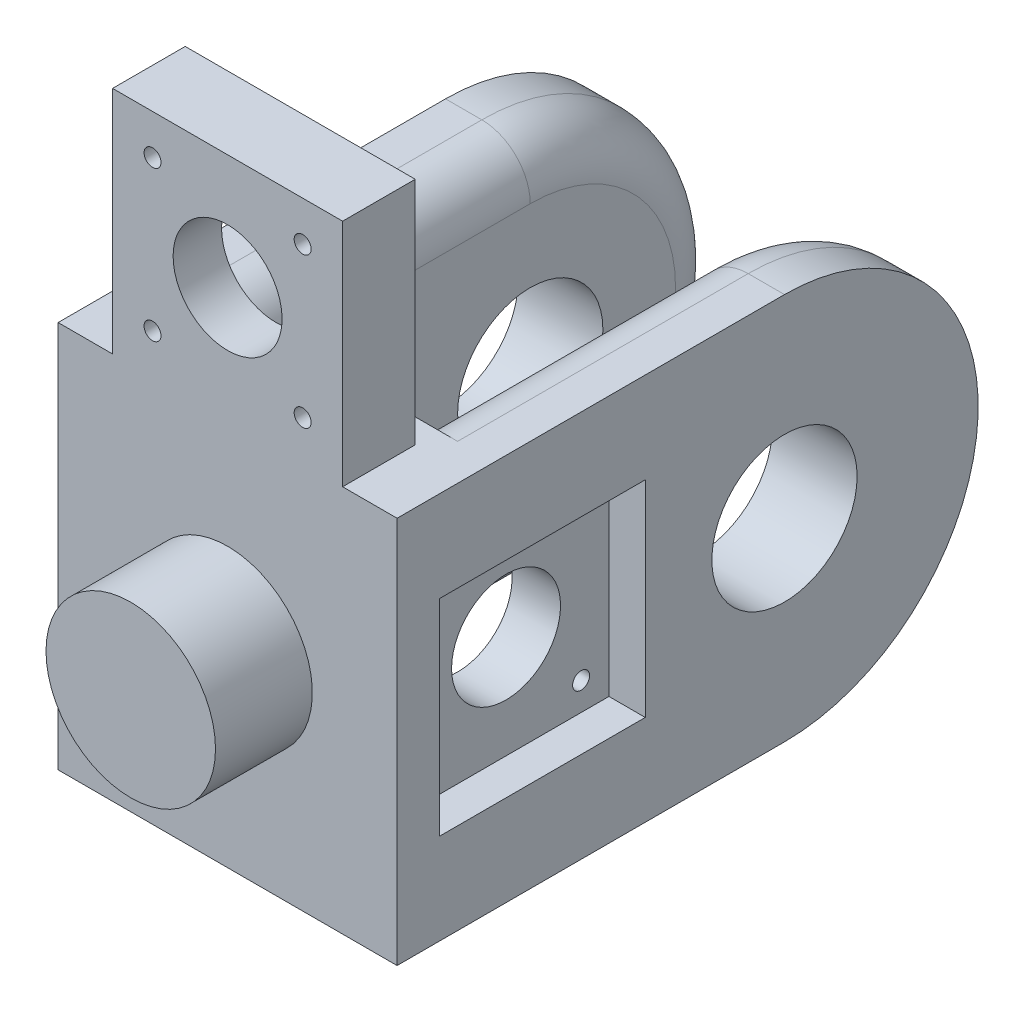
SolidWorks part; units mm, degrees
ref_plane "Front Plane" through (0, 0, 0) normal (0, 0, 1) x (1, 0, 0)
ref_plane "Top Plane" through (0, 0, 0) normal (0, 1, 0) x (1, 0, 0)
ref_plane "Right Plane" through (0, 0, 0) normal (1, 0, 0) x (0, 0, -1)
sketch "Sketch1" plane through (0, 0, 0) normal (0, 0, 1) x (1, 0, 0)
  line L0 (-17.5, 40) -> (-35, 40)
  line L2 (-17.5, -40) -> (-17.5, 40)
  line L4 (17.5, -40) -> (17.5, 40)
  line L5 (-17.5, -40) -> (17.5, 40) construction
  line L6 (-17.5, 40) -> (17.5, -40) construction
  line L7 (35, -40) -> (17.5, -40)
  line L8 (35, -40) -> (35, 40)
  line L9 (35, 40) -> (17.5, 40)
  line L10 (-35, -40) -> (-35, 40)
  line L11 (35, -40) -> (-35, 40) construction
  line L12 (35, 40) -> (-35, -40) construction
  line L13 (-17.5, -40) -> (-35, -40)
  point P0 (0, 0)
  point P6 (0, 0)
  dimension "D1" = 80
  dimension "D2" = 35
  dimension "D3" = 70
extrude "Boss-Extrude1" add sketch "Sketch1" along normal blind 100
sketch "Sketch2" plane through (0, 0, 100) normal (0, 0, 1) x (1, 0, 0)
  line L0 (-35, 40) -> (35, 40)
  line L1 (35, 40) -> (35, -40)
  line L2 (35, -40) -> (-35, -40)
  line L3 (-35, -40) -> (-35, 40)
extrude "Boss-Extrude2" add sketch "Sketch2" along normal blind 20
sketch "Sketch3" plane through (35, 0, 0) normal (1, 0, 0) x (0, 0, -1)
  line L0 (0, 0) -> (-80, 0) construction
  line L2 (-40, 40) -> (0, 40)
  line L3 (0, 40) -> (0, 0)
  line L4 (0, 0) -> (0, -40)
  line L5 (0, -40) -> (-40, -40)
  arc A0 (-40, -40) -> (-40, 40) centre (-40, 0) ccw
  circle A1 centre (-40, 0) radius 15
  line M2 (0, -40) -> (0, 40)
  line M3 (0, 40) -> (-120, 40)
  line M5 (-120, -40) -> (0, -40)
  dimension "D2" = 30
  dimension "D1" = 80
extrude "Cut-Extrude1" cut sketch "Sketch3" against normal through all both and the other way through all contours A1 L0 | L0 A1 | A0 M2 M3 | A0 M5 M2
sketch "Sketch5" plane through (-35, 0, 0) normal (-1, 0, 0) x (0, 0, 1)
  line L0 (0, 0) -> (90, 0) construction
  circle A2 centre (90, 0) radius 11.25
  dimension "D1" = 22.5
  dimension "D2" = 90
extrude "Cut-Extrude2" cut sketch "Sketch5" against normal through all both and the other way through all
sketch "Sketch6" plane through (35, 0, 0) normal (1, 0, 0) x (0, 0, -1)
  line L5 (-111.25, -21.25) -> (-68.75, -21.25)
  line L6 (-111.25, -21.25) -> (-111.25, 21.25)
  line L7 (-111.25, 21.25) -> (-68.75, 21.25)
  line L8 (-68.75, -21.25) -> (-68.75, 21.25)
  line L9 (-111.25, -21.25) -> (-68.75, 21.25) construction
  line L10 (-111.25, 21.25) -> (-68.75, -21.25) construction
  point P0 (-90, 0)
  dimension "D1" = 42.5
  dimension "D2" = 42.5
extrude "Cut-Extrude3" cut sketch "Sketch6" against normal blind 7.5
sketch "Sketch7" plane through (35, 0, 0) normal (1, 0, 0) x (0, 0, -1)
  line L5 (-74.5, -15.5) -> (-105.5, -15.5) construction
  line L6 (-74.5, -15.5) -> (-74.5, 15.5) construction
  line L7 (-74.5, 15.5) -> (-105.5, 15.5) construction
  line L8 (-105.5, -15.5) -> (-105.5, 15.5) construction
  line L9 (-74.5, -15.5) -> (-105.5, 15.5) construction
  line L10 (-74.5, 15.5) -> (-105.5, -15.5) construction
  circle A4 centre (-105.5, 15.5) radius 1.75
  circle A5 centre (-74.5, 15.5) radius 1.75
  circle A6 centre (-74.5, -15.5) radius 1.75
  circle A7 centre (-105.5, -15.5) radius 1.75
  point P0 (-90, 0)
  dimension "D3" = 3.5
  dimension "D1" = 31
  dimension "D2" = 31
extrude "Cut-Extrude4" cut sketch "Sketch7" against normal through all both and the other way through all
sketch "Sketch8" plane through (-35, 0, 0) normal (-1, 0, 0) x (0, 0, 1)
  line L5 (111.25, -21.25) -> (68.75, -21.25)
  line L6 (111.25, -21.25) -> (111.25, 21.25)
  line L7 (111.25, 21.25) -> (68.75, 21.25)
  line L8 (68.75, -21.25) -> (68.75, 21.25)
  line L9 (111.25, -21.25) -> (68.75, 21.25) construction
  line L10 (111.25, 21.25) -> (68.75, -21.25) construction
  point P0 (90, 0)
  dimension "D1" = 42.5
  dimension "D2" = 42.5
extrude "Cut-Extrude5" cut sketch "Sketch8" against normal blind 7.5
sketch "Sketch9" plane through (17.5, 0, 0) normal (-1, 0, 0) x (0, 0, 1)
  line L6 (105.5, 19.25) -> (95.9631, 19.25)
  line L7 (95.9631, 19.25) -> (95.9631, 11.75)
  line L8 (95.9631, 11.75) -> (105.5, 11.75)
  line L9 (105.5, -11.75) -> (95.9631, -11.75)
  line L10 (95.9631, -11.75) -> (95.9631, -19.25)
  line L11 (95.9631, -19.25) -> (105.5, -19.25)
  arc A2 (105.5, 11.75) -> (105.5, 19.25) centre (105.5, 15.5) ccw
  arc A3 (105.5, -19.25) -> (105.5, -11.75) centre (105.5, -15.5) ccw
  dimension "D1" = 7.5
  dimension "D2" = 7.5
extrude "Cut-Extrude7" cut sketch "Sketch9" along normal blind 35
sketch "Sketch10" plane through (0, 40, 0) normal (0, 1, 0) x (1, 0, 0)
  line L0 (23.75, -105) -> (-23.75, -105)
  line L1 (17.5, -100) -> (-17.5, -100) construction
  line L3 (0, -110) -> (0, -100) construction
  line L4 (-23.75, -105) -> (-23.75, -120)
  line L5 (35, -120) -> (-35, -120) construction
  line L6 (-23.75, -120) -> (23.75, -120)
  line L7 (23.75, -120) -> (23.75, -105)
  point P7 (0, -105)
  point P9 (0, -110)
  dimension "D1" = 47.5
extrude "Boss-Extrude3" add sketch "Sketch10" along normal blind 47.5
sketch "Sketch11" plane through (0, 0, 105) normal (0, 0, -1) x (-1, 0, 0)
  line L0 (-23.75, 87.5) -> (23.75, 40) construction
  line L2 (15.5, 48.25) -> (-15.5, 48.25) construction
  line L3 (15.5, 48.25) -> (15.5, 79.25) construction
  line L4 (15.5, 79.25) -> (-15.5, 79.25) construction
  line L5 (-15.5, 48.25) -> (-15.5, 79.25) construction
  line L6 (15.5, 48.25) -> (-15.5, 79.25) construction
  line L7 (15.5, 79.25) -> (-15.5, 48.25) construction
  circle A0 centre (0, 63.75) radius 11.25
  circle A1 centre (15.5, 79.25) radius 1.75
  circle A2 centre (15.5, 48.25) radius 1.75
  circle A3 centre (-15.5, 48.25) radius 1.75
  circle A4 centre (-15.5, 79.25) radius 1.75
  point P4 (0, 63.75)
  dimension "D2" = 22.5
  dimension "D3" = 3.5
  dimension "D1" = 31
extrude "Cut-Extrude8" cut sketch "Sketch11" against normal through all
sketch "Sketch12" plane through (0, 0, 105) normal (0, 0, -1) x (-1, 0, 0)
  line L1 (21.25, 42.5) -> (-21.25, 42.5)
  line L2 (21.25, 42.5) -> (21.25, 85)
  line L3 (21.25, 85) -> (-21.25, 85)
  line L4 (-21.25, 42.5) -> (-21.25, 85)
  line L5 (21.25, 42.5) -> (-21.25, 85) construction
  line L6 (21.25, 85) -> (-21.25, 42.5) construction
  point P0 (0, 63.75)
  dimension "D1" = 42.5
  dimension "D2" = 42.5
extrude "Cut-Extrude9" cut sketch "Sketch12" against normal blind 5
sketch "Sketch13" plane through (0, 0, 120) normal (0, 0, 1) x (1, 0, 0)
  circle A0 centre (0, 0) radius 17.5
  dimension "D1" = 35
extrude "Boss-Extrude4" add sketch "Sketch13" along normal blind 20
fillet "Fillet1" radius 10 6 edges at (-17.5, 40, 70) (-17.5, -40, 70) (17.5, -40, 70) (17.5, 40, 70) (-17.5, 0, 0) (17.5, 0, 0)
